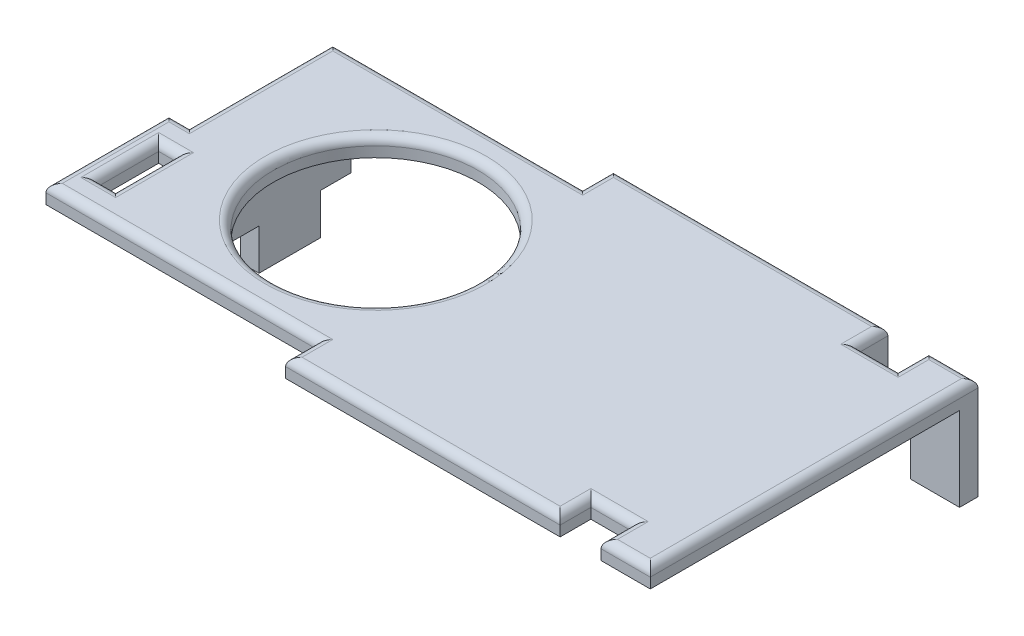
SolidWorks part; units mm, degrees
material "Plain Carbon Steel"
ref_plane "Front Plane" through (0, 0, 0) normal (0, 0, 1) x (1, 0, 0)
ref_plane "Top Plane" through (0, 0, 0) normal (0, 1, 0) x (1, 0, 0)
ref_plane "Right Plane" through (0, 0, 0) normal (1, 0, 0) x (0, 0, -1)
sketch "Sketch2" plane through (0, 0, 0) normal (0, 1, 0) x (1, 0, 0)
  line L0 (0, 0) -> (-57.9752, 0) construction
  line L1 (0, -10.16) -> (0, 10.16)
  line L2 (0, 10.16) -> (-3.048, 10.16)
  line L3 (-3.048, 10.16) -> (-3.048, 8.255)
  line L4 (-3.048, 8.255) -> (-5.588, 8.255)
  line L5 (-5.588, 8.255) -> (-5.588, 10.16)
  line L6 (-5.588, 10.16) -> (-22.606, 10.16)
  line L7 (-22.606, 10.16) -> (-22.606, 8.255)
  line L8 (-22.606, 8.255) -> (-38.1, 8.255)
  line L9 (0, -10.16) -> (-3.048, -10.16)
  line L10 (-3.048, -10.16) -> (-3.048, -8.255)
  line L11 (-3.048, -8.255) -> (-5.588, -8.255)
  line L12 (-5.588, -8.255) -> (-5.588, -10.16)
  line L13 (-5.588, -10.16) -> (-22.606, -10.16)
  line L14 (-22.606, -10.16) -> (-22.606, -8.255)
  line L15 (-22.606, -8.255) -> (-38.1, -8.255)
  line L16 (-38.1, -8.255) -> (-39.37, -8.255)
  line L17 (-39.37, -8.255) -> (-39.37, -0.635)
  line L18 (-39.37, -0.635) -> (-38.1, -0.635)
  line L19 (-38.1, -0.635) -> (-38.1, 8.255)
  dimension "D1" = 10.16
  dimension "D2" = 3.048
  dimension "D3" = 2.54
  dimension "D4" = 17.018
  dimension "D5" = 15.494
  dimension "D6" = 1.905
  dimension "D7" = 7.62
  dimension "D8" = 1.27
extrude "Boss-Extrude1" add sketch "Sketch2" along normal blind 1.143
sketch "Sketch3" plane through (0, 1.143, 0) normal (0, 1, 0) x (1, 0, 0)
  line L0 (0, -10.16) -> (0, 10.16) construction
  line L1 (-5.588, 10.16) -> (-14.605, 10.16)
  line L2 (-5.588, 10.16) -> (-5.588, 9.017)
  line L3 (-5.588, 9.017) -> (-14.605, 9.017)
  line L4 (-14.605, 10.16) -> (-14.605, 9.017)
  line L5 (-3.048, 10.16) -> (0, 10.16)
  line L6 (-3.048, 10.16) -> (-3.048, 9.017)
  line L7 (-3.048, 9.017) -> (0, 9.017)
  line L8 (0, 10.16) -> (0, 9.017)
  dimension "D1" = 9.017
  dimension "D2" = 1.143
extrude "Boss-Extrude2" add sketch "Sketch3" against normal blind 6.35
sketch "Sketch4" plane through (-38.1, 0, 0) normal (-1, 0, 0) x (0, 0, 1)
  line L0 (-4.445, 1.143) -> (-4.445, -8.5268) construction
  line L1 (-8.255, 1.143) -> (-0.635, 1.143)
  line L2 (-8.255, 1.143) -> (0.635, 1.143) construction
  line L3 (-8.255, 1.143) -> (-8.255, -5.334)
  line L4 (-8.255, -5.334) -> (-6.35, -5.334)
  line L5 (-6.35, -5.334) -> (-6.35, -7.874)
  line L6 (-6.35, -7.874) -> (-2.54, -7.874)
  line L7 (-2.54, -5.334) -> (-2.54, -7.874)
  line L8 (-0.635, -5.334) -> (-2.54, -5.334)
  line L9 (-0.635, 1.143) -> (-0.635, -5.334)
  point P11 (-4.445, -7.874)
  dimension "D1" = 1.905
  dimension "D2" = 2.54
  dimension "D3" = 1.905
  dimension "D4" = 6.477
extrude "Boss-Extrude4" add sketch "Sketch4" against normal blind 1.143
sketch "Sketch5" plane through (0, 0, 0) normal (0, 1, 0) x (1, 0, 0)
  line L0 (0, 0) -> (-41.9639, 0) construction
  line L1 (-39.37, -0.635) -> (-39.37, -8.255) construction
  line L2 (-38.1, -2.54) -> (-36.957, -2.54)
  line L3 (-38.1, -2.54) -> (-38.1, -6.35)
  line L4 (-38.1, -6.35) -> (-36.957, -6.35)
  line L5 (-36.957, -2.54) -> (-36.957, -6.35)
  line L6 (-39.37, -8.255) -> (-22.606, -8.255) construction
  circle A0 centre (-27.178, 0) radius 6.35
  dimension "D1" = 12.7
  dimension "D2" = 27.178
  dimension "D3" = 1.143
  dimension "D4" = 1.27
  dimension "D5" = 3.81
  dimension "D6" = 1.905
extrude "Cut-Extrude2" cut sketch "Sketch5" along normal through all
fillet "Fillet1" radius 0.508 23 edges at (-27.178, 1.143, 6.35) (-30.353, 1.143, -8.255) (-22.606, 1.143, -9.2075) (-14.097, 1.143, -10.16) (-5.588, 1.143, -9.2075) (-4.318, 1.143, -8.255) (-3.048, 1.143, -9.2075) (-1.524, 1.143, -10.16) (0, 1.143, 0) (-1.524, 1.143, 10.16) (-3.048, 1.143, 9.2075) (-4.318, 1.143, 8.255) (-5.588, 1.143, 9.2075) (-14.097, 1.143, 10.16) (-22.606, 1.143, 9.2075) (-30.988, 1.143, 8.255) (-39.37, 1.143, 4.445) (-38.735, 1.143, 0.635) (-38.1, 1.143, -3.81) (-36.957, 1.143, 4.445) (-37.5285, 1.143, 2.54) (-38.1, 1.143, 4.445) (-37.5285, 1.143, 6.35)
sketch "Sketch6" plane through (0, 0, 0) normal (0, 1, 0) x (1, 0, 0)
  text T0 "Chenyang Wang" font "Times New Roman" height in points 7
wrap "Wrap1" [suppressed] sketch "Sketch6" source sketch "Sketch6" thickness 0.254 parameters "D1"=0.254
